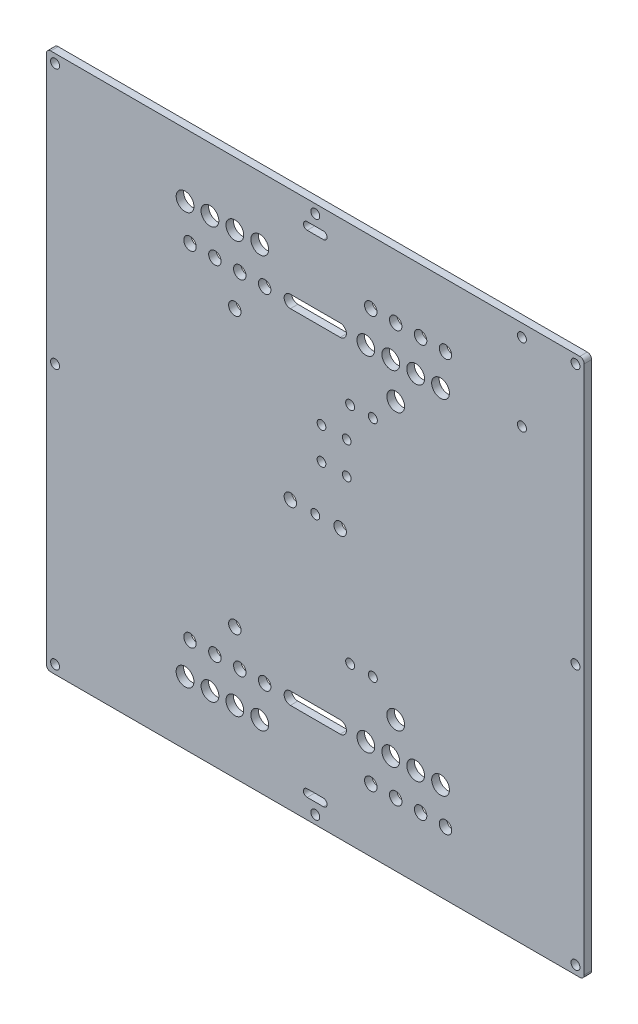
SolidWorks part; units mm, degrees
ref_plane "Front Plane" through (0, 0, 0) normal (0, 0, 1) x (1, 0, 0)
ref_plane "Top Plane" through (0, 0, 0) normal (0, 1, 0) x (1, 0, 0)
ref_plane "Right Plane" through (0, 0, 0) normal (1, 0, 0) x (0, 0, -1)
sketch "Sketch1" plane through (0, 0, 0) normal (0, 0, 1) x (1, 0, 0)
  line L0 (-3.25, -98.62) -> (3.25, -98.62) construction
  line L1 (-106.25, -108) -> (106.25, -108)
  line L2 (-108, -106.25) -> (-108, 106.25)
  line L3 (-106.25, 108) -> (106.25, 108)
  line L4 (108, -106.25) -> (108, 106.25)
  line L5 (-108, -108) -> (108, 108) construction
  line L6 (-108, 108) -> (108, -108) construction
  line L7 (-3.25, -97.12) -> (3.25, -97.12)
  line L8 (-3.25, -100.12) -> (3.25, -100.12)
  line L9 (0, -98.62) -> (0, -104.5) construction
  line L10 (-10, -69) -> (10, -69) construction
  line L11 (-10, -66.5) -> (10, -66.5)
  line L12 (-10, -71.5) -> (10, -71.5)
  line L13 (0, -69) -> (0, -98.62) construction
  line L14 (-32.3, -55.35) -> (32.3, -55.35) construction
  line L15 (32.3, -55.35) -> (0, -55.35) construction
  line L16 (0, -55.35) -> (0, -69) construction
  line L17 (-108, 0) -> (108, 0) construction
  line L18 (14, -45) -> (23.12, -45) construction
  line L19 (-10, 0) -> (10, 0) construction
  line L20 (-3.25, 98.62) -> (3.25, 98.62) construction
  line L21 (-3.25, 97.12) -> (3.25, 97.12)
  line L22 (-3.25, 100.12) -> (3.25, 100.12)
  line L23 (-10, 69) -> (10, 69) construction
  line L24 (-10, 66.5) -> (10, 66.5)
  line L25 (-10, 71.5) -> (10, 71.5)
  line L26 (14, 45) -> (23.12, 45) construction
  line L27 (0, 55.35) -> (0, 69) construction
  line L28 (32.3, 55.35) -> (0, 55.35) construction
  line L29 (-32.3, 55.35) -> (32.3, 55.35) construction
  line L30 (0, 69) -> (0, 98.62) construction
  line L31 (83, 103) -> (83, 72) construction
  arc A0 (-106.25, -108) -> (-108, -106.25) centre (-106.25, -106.25) cw
  arc A1 (106.25, -108) -> (108, -106.25) centre (106.25, -106.25) ccw
  arc A2 (106.25, 108) -> (108, 106.25) centre (106.25, 106.25) cw
  arc A3 (-108, 106.25) -> (-106.25, 108) centre (-106.25, 106.25) cw
  circle A4 centre (-104.5, 104.5) radius 1.8
  circle A5 centre (0, 104.5) radius 1.8
  circle A6 centre (104.5, 104.5) radius 1.8
  circle A7 centre (-104.5, 0) radius 1.8
  circle A8 centre (0, 0) radius 1.8
  circle A9 centre (104.5, 0) radius 1.8
  circle A10 centre (-104.5, -104.5) radius 1.8
  circle A11 centre (0, -104.5) radius 1.8
  circle A12 centre (104.5, -104.5) radius 1.8
  circle A13 centre (-52.3, -82.65) radius 3.57
  circle A14 centre (-42.3, -82.65) radius 3.57
  circle A15 centre (-32.3, -82.65) radius 3.57
  circle A16 centre (-22.3, -82.65) radius 3.57
  arc A17 (-3.25, -97.12) -> (-3.25, -100.12) centre (-3.25, -98.62) ccw
  arc A18 (3.25, -100.12) -> (3.25, -97.12) centre (3.25, -98.62) ccw
  circle A19 centre (-50.32, -69) radius 2.5
  circle A20 centre (-40.32, -69) radius 2.5
  circle A21 centre (-30.32, -69) radius 2.5
  circle A22 centre (-20.32, -69) radius 2.5
  arc A23 (-10, -66.5) -> (-10, -71.5) centre (-10, -69) ccw
  arc A24 (10, -71.5) -> (10, -66.5) centre (10, -69) ccw
  circle A25 centre (42.3, -82.65) radius 2.5
  circle A26 centre (32.3, -82.65) radius 2.5
  circle A27 centre (22.3, -82.65) radius 2.5
  circle A28 centre (52.3, -82.65) radius 2.5
  circle A29 centre (50.32, -69) radius 3.57
  circle A30 centre (40.32, -69) radius 3.57
  circle A31 centre (30.32, -69) radius 3.57
  circle A32 centre (20.32, -69) radius 3.57
  circle A33 centre (-32.3, -55.35) radius 2.5
  circle A34 centre (32.3, -55.35) radius 3.57
  circle A35 centre (14, -45) radius 1.8
  circle A36 centre (23.12, -45) radius 1.8
  circle A37 centre (-10, 0) radius 2.5
  circle A38 centre (10, 0) radius 2.5
  circle A39 centre (2.5, 32.3) radius 1.75
  circle A40 centre (12.64, 32.3) radius 1.75
  circle A41 centre (2.5, 19.47) radius 1.75
  circle A42 centre (12.64, 19.47) radius 1.75
  arc A43 (-3.25, 97.12) -> (-3.25, 100.12) centre (-3.25, 98.62) cw
  arc A44 (3.25, 100.12) -> (3.25, 97.12) centre (3.25, 98.62) cw
  arc A45 (-10, 66.5) -> (-10, 71.5) centre (-10, 69) cw
  arc A46 (10, 71.5) -> (10, 66.5) centre (10, 69) cw
  circle A47 centre (23.12, 45) radius 1.8
  circle A48 centre (14, 45) radius 1.8
  circle A49 centre (32.3, 55.35) radius 3.57
  circle A50 centre (-32.3, 55.35) radius 2.5
  circle A51 centre (20.32, 69) radius 3.57
  circle A52 centre (30.32, 69) radius 3.57
  circle A53 centre (40.32, 69) radius 3.57
  circle A54 centre (50.32, 69) radius 3.57
  circle A55 centre (52.3, 82.65) radius 2.5
  circle A56 centre (22.3, 82.65) radius 2.5
  circle A57 centre (32.3, 82.65) radius 2.5
  circle A58 centre (42.3, 82.65) radius 2.5
  circle A59 centre (-20.32, 69) radius 2.5
  circle A60 centre (-30.32, 69) radius 2.5
  circle A61 centre (-40.32, 69) radius 2.5
  circle A62 centre (-50.32, 69) radius 2.5
  circle A63 centre (-22.3, 82.65) radius 3.57
  circle A64 centre (-32.3, 82.65) radius 3.57
  circle A65 centre (-42.3, 82.65) radius 3.57
  circle A66 centre (-52.3, 82.65) radius 3.57
  circle A67 centre (83, 103) radius 1.8
  circle A68 centre (83, 72) radius 1.8
  point P0 (0, 0)
  point P45 (0, -98.62)
  point P61 (0, -69)
  point P108 (0, 98.62)
  point P115 (0, 69)
  dimension "D2" = 1.75
  dimension "D3" = 3.6
  dimension "D5" = 7.14
  dimension "D12" = 5
  dimension "D19" = 5
  dimension "D21" = 7.14
  dimension "D24" = 5
  dimension "D25" = 7.14
  dimension "D28" = 3.6
  dimension "D29" = 3.6
  dimension "D33" = 5
  dimension "D34" = 5
  dimension "D37" = 3.5
  dimension "D43" = 3.6
  dimension "D44" = 3.6
  dimension "D1" = 216
  dimension "D4" = 104.5
  dimension "D6" = 160.3
  dimension "D7" = 25.35
  dimension "D8" = 10
  dimension "D9" = 6.5
  dimension "D10" = 3
  dimension "D11" = 9.38
  dimension "D13" = 158.32
  dimension "D14" = 39
  dimension "D15" = 10
  dimension "D16" = 5
  dimension "D17" = 20
  dimension "D18" = 55.7
  dimension "D20" = 10
  dimension "D22" = 57.68
  dimension "D23" = 10
  dimension "D26" = 64.6
  dimension "D27" = 110.7
  dimension "D30" = 9.12
  dimension "D31" = 63
  dimension "D32" = 122
  dimension "D35" = 10
  dimension "D36" = 10
  dimension "D38" = 10.14
  dimension "D39" = 12.83
  dimension "D40" = 75.7
  dimension "D41" = 110.5
  dimension "D42" = 21.5
  dimension "D45" = 36
  dimension "D46" = 31
extrude "Boss-Extrude1" add sketch "Sketch1" along normal mid plane 3
